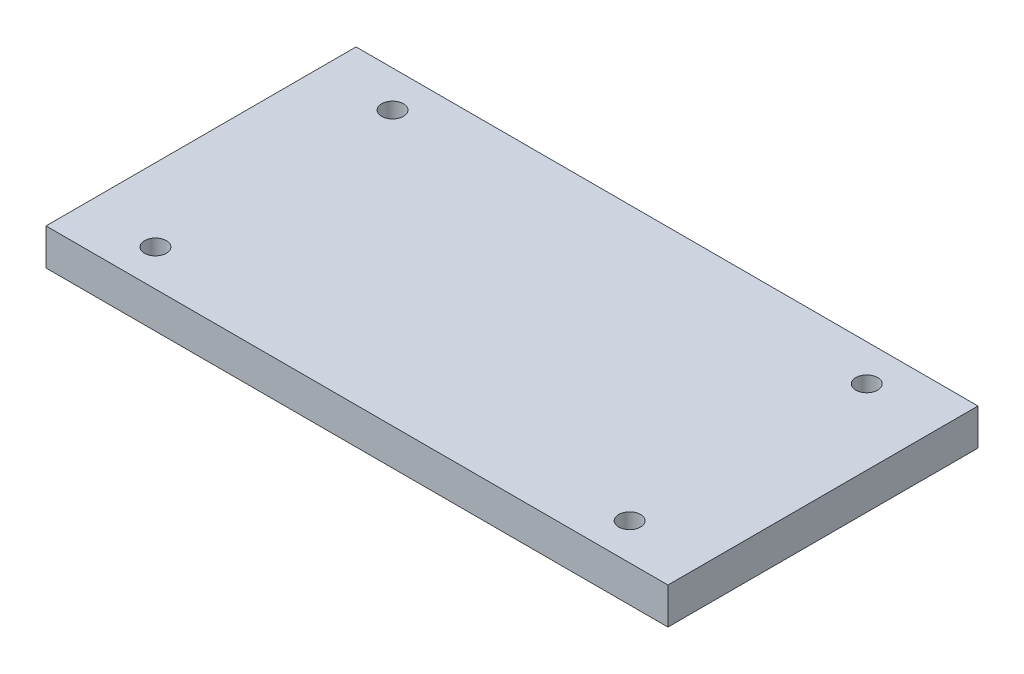
SolidWorks part; units mm, degrees
ref_plane "Front Plane" through (0, 0, 0) normal (0, 0, 1) x (1, 0, 0)
ref_plane "Top Plane" through (0, 0, 0) normal (0, 1, 0) x (1, 0, 0)
ref_plane "Right Plane" through (0, 0, 0) normal (1, 0, 0) x (0, 0, -1)
sketch "Sketch1" plane through (0, 0, 0) normal (0, 1, 0) x (1, 0, 0)
  line L1 (0, 85) -> (170.5, 85)
  line L2 (0, 85) -> (0, 0)
  line L3 (0, 0) -> (170.5, 0)
  line L4 (170.5, 85) -> (170.5, 0)
  circle A0 centre (20, 10) radius 3
  circle A1 centre (150, 10) radius 3
  circle A3 centre (20, 75) radius 3
  circle A5 centre (150, 75) radius 3
extrude "Boss-Extrude1" add sketch "Sketch1" along normal blind 10
